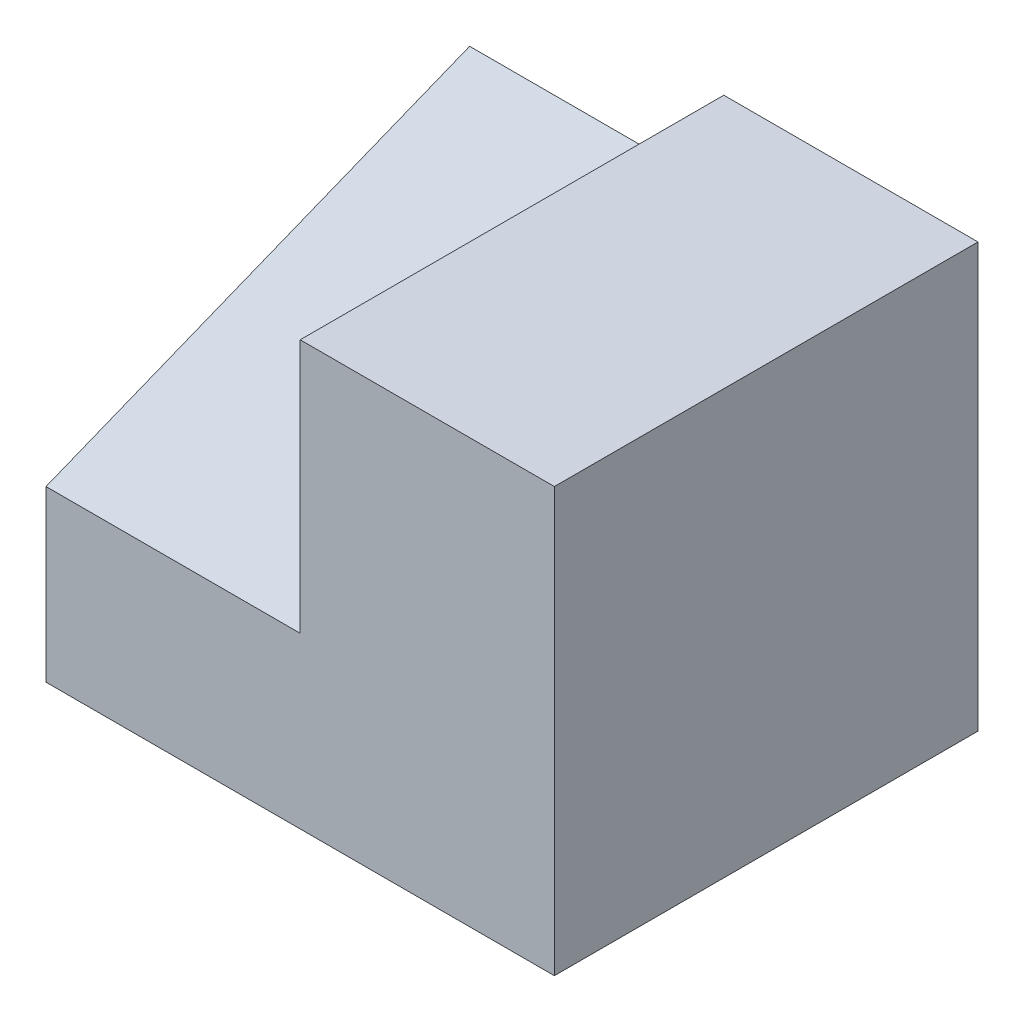
SolidWorks part; units mm, degrees
ref_plane "Front Plane" through (0, 0, 0) normal (0, 0, 1) x (1, 0, 0)
ref_plane "Top Plane" through (0, 0, 0) normal (0, 1, 0) x (1, 0, 0)
ref_plane "Right Plane" through (0, 0, 0) normal (1, 0, 0) x (0, 0, -1)
sketch "Sketch1" plane through (0, 0, 0) normal (0, 0, 1) x (1, 0, 0)
  line L0 (-15, 25) -> (0, 25)
  line L1 (0, 25) -> (0, 0)
  line L2 (0, 0) -> (-30, 0)
  line L3 (-30, 0) -> (-30, 10)
  line L4 (-30, 10) -> (-15, 10)
  line L5 (-15, 10) -> (-15, 25)
  dimension "D1" = 15
  dimension "D2" = 25
  dimension "D3" = 15
  dimension "D4" = 30
extrude "Boss-Extrude1" add sketch "Sketch1" along normal blind 25
sketch "Sketch5" plane through (-15, 0, 0) normal (-1, 0, 0) x (0, 0, 1)
  line L0 (0, 10) -> (0, 20)
  line L1 (0, 25) -> (0, 10) construction
  line L2 (0, 20) -> (25, 10)
  line L3 (25, 10) -> (0, 10)
  dimension "D1" = 10
extrude "Boss-Extrude4" add sketch "Sketch5" along normal blind 15
